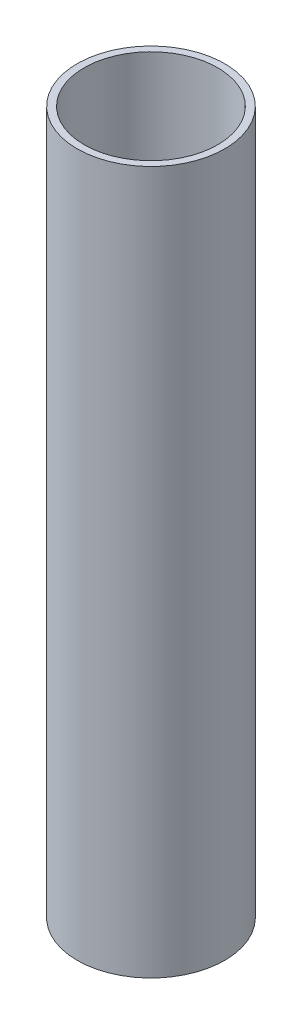
SolidWorks part; units mm, degrees
ref_plane "Front Plane" through (0, 0, 0) normal (0, 0, 1) x (1, 0, 0)
ref_plane "Top Plane" through (0, 0, 0) normal (0, 1, 0) x (1, 0, 0)
ref_plane "Right Plane" through (0, 0, 0) normal (1, 0, 0) x (0, 0, -1)
sketch "Sketch1" plane through (0, 0, 0) normal (0, 1, 0) x (1, 0, 0)
  circle A0 centre (0, 0) radius 21
  circle A1 centre (0, 0) radius 19
extrude "Boss-Extrude1" add sketch "Sketch1" along normal blind 200
